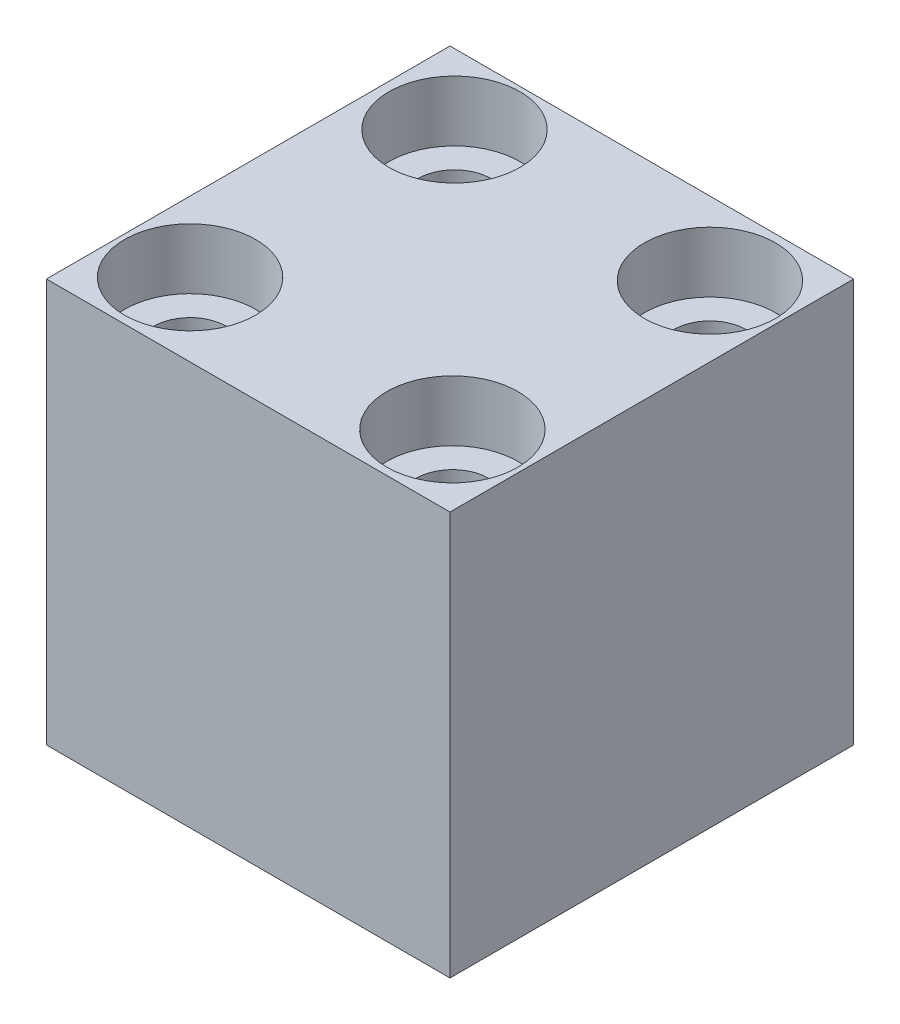
SolidWorks part; units mm, degrees
ref_plane "Plano frontal" through (0, 0, 0) normal (0, 0, 1) x (1, 0, 0)
ref_plane "Plano superior" through (0, 0, 0) normal (0, 1, 0) x (1, 0, 0)
ref_plane "Plano direito" through (0, 0, 0) normal (1, 0, 0) x (0, 0, -1)
sketch "Esboço1" plane through (0, 0, 0) normal (0, 1, 0) x (1, 0, 0)
  line L1 (-10, -10) -> (10, -10)
  line L2 (-10, -10) -> (-10, 10)
  line L3 (-10, 10) -> (10, 10)
  line L4 (10, -10) -> (10, 10)
  line L5 (-10, -10) -> (10, 10) construction
  line L6 (-10, 10) -> (10, -10) construction
  point P0 (0, 0)
  dimension "D1" = 20
  dimension "D2" = 20
extrude "Ressalto-extrusão1" add sketch "Esboço1" along normal blind 20
sketch "Esboço2" plane through (0, 0, 0) normal (0, 1, 0) x (1, 0, 0)
  point P0 (-7.0094, 6.8394)
  point P1 (6.9048, 6.8394)
  point P2 (6.9048, -6.7871)
  point P3 (-6.7217, -6.7871)
hole_wizard "Rebaixo para SHCS M32" positions "3DSketch3" profile "Esboço5" counterbore size "M3" standard "Ansi Metric" end condition through all
sketch3d "3DSketch3"
  point P0 (-6.3032, 20, -6.5256)
  point P2 (6.5125, 20, -6.3686)
  point P4 (6.5125, 20, 6.3948)
  point P6 (-6.5125, 20, 6.3686)
sketch "Esboço5" plane through (-6.3032, 20, -6.5256) normal (1, 0, 0) x (0, 0, 1)
  line L0 (0, 0) -> (0, 20)
  line L1 (0, 20) -> (1.8, 20)
  line L3 (1.8, 20) -> (1.8, 3)
  line L4 (1.8, 3) -> (3.25, 3)
  line L5 (3.25, 3) -> (3.25, 0)
  line L7 (3.25, 0) -> (0, 0)
  line L11 (0, -6.35) -> (0, 107.95) construction
  dimension "Thru Hole Dia." = 3.6
  dimension "Thru Hole Depth" = 20
  dimension "C'Bore Dia." = 6.5
  dimension "C'Bore Depth" = 3
